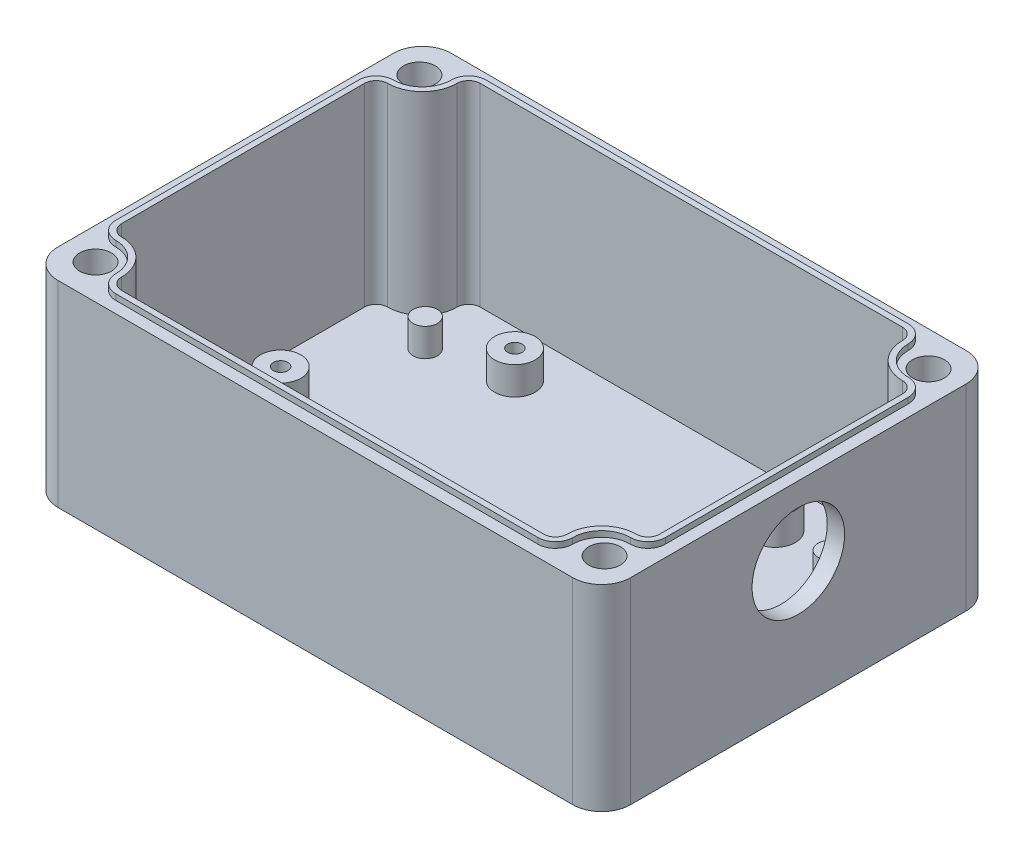
SolidWorks part; units mm, degrees
ref_plane "Plan de face" through (0, 0, 0) normal (0, 0, 1) x (1, 0, 0)
ref_plane "Plan de dessus" through (0, 0, 0) normal (0, 1, 0) x (1, 0, 0)
ref_plane "Plan de droite" through (0, 0, 0) normal (1, 0, 0) x (0, 0, -1)
sketch "Esquisse1" plane through (0, 0, 0) normal (0, 1, 0) x (1, 0, 0)
  line L1 (-44.5, 34) -> (44.5, 34)
  line L2 (-49.5, 29) -> (-49.5, -29)
  line L3 (-44.5, -34) -> (44.5, -34)
  line L4 (49.5, 29) -> (49.5, -29)
  arc A0 (49.5, 29) -> (44.5, 34) centre (44.5, 29) ccw
  arc A1 (44.5, -34) -> (49.5, -29) centre (44.5, -29) ccw
  arc A2 (-49.5, -29) -> (-44.5, -34) centre (-44.5, -29) ccw
  arc A3 (-49.5, 29) -> (-44.5, 34) centre (-44.5, 29) cw
  point P7 (49.5, 34)
  point P12 (-49.5, -34)
  point P15 (-49.5, 34)
  dimension "D5" = 5
  dimension "D1" = 68
  dimension "D2" = 99
  dimension "D3" = 49.5
  dimension "D4" = 34
extrude "Boss.-Extru.1" add sketch "Esquisse1" along normal blind 34
sketch "Esquisse2" plane through (0, 34, 0) normal (0, 1, 0) x (1, 0, 0)
  line L0 (-36.5, 31) -> (36.5, 31)
  line L1 (-46.5, 21) -> (-46.5, -21)
  line L2 (-36.5, -31) -> (36.5, -31)
  line L3 (46.5, 21) -> (46.5, -21)
  line L4 (-49.5, 29) -> (-49.5, -29) construction
  line L5 (49.5, -29) -> (49.5, 29) construction
  line L6 (-44.5, -34) -> (44.5, -34) construction
  line L7 (44.5, 34) -> (-44.5, 34) construction
  arc A0 (-44.5, -23) -> (-38.5, -29) centre (-44.5, -29) cw
  arc A1 (-38.5, 29) -> (-44.5, 23) centre (-44.5, 29) cw
  arc A2 (38.5, 29) -> (44.5, 23) centre (44.5, 29) ccw
  arc A3 (44.5, -23) -> (38.5, -29) centre (44.5, -29) ccw
  arc A4 (38.5, 29) -> (36.5, 31) centre (36.5, 29) ccw
  arc A5 (46.5, 21) -> (44.5, 23) centre (44.5, 21) ccw
  arc A6 (44.5, -23) -> (46.5, -21) centre (44.5, -21) ccw
  arc A7 (36.5, -31) -> (38.5, -29) centre (36.5, -29) ccw
  arc A8 (-38.5, -29) -> (-36.5, -31) centre (-36.5, -29) ccw
  arc A9 (-44.5, -23) -> (-46.5, -21) centre (-44.5, -21) cw
  arc A10 (-46.5, 21) -> (-44.5, 23) centre (-44.5, 21) cw
  arc A11 (-38.5, 29) -> (-36.5, 31) centre (-36.5, 29) cw
  point P26 (38.8431, 31)
  point P29 (46.5, 23.3431)
  point P32 (46.5, -23.3431)
  point P35 (38.8431, -31)
  point P38 (-38.8431, -31)
  point P41 (-46.5, -23.3431)
  point P44 (-46.5, 23.3431)
  point P47 (-38.8431, 31)
  dimension "D9" = 6
  dimension "D10" = 2
  dimension "D1" = 3
  dimension "D2" = 3
  dimension "D3" = 3
  dimension "D4" = 3
  dimension "D5" = 5
  dimension "D6" = 5
  dimension "D7" = 5
  dimension "D8" = 5
extrude "Enlèv. mat.-Extru.1" cut sketch "Esquisse2" against normal blind 32.5
sketch "Esquisse3" plane through (0, 34, 0) normal (0, 1, 0) x (1, 0, 0)
  circle A0 centre (-44, 28) radius 2.75
  circle A1 centre (-44, -28) radius 2.75
  circle A2 centre (44, -28) radius 2.75
  circle A3 centre (44, 28) radius 2.75
  dimension "D1" = 5.5
  dimension "D2" = 28
  dimension "D3" = 56
  dimension "D4" = 88
  dimension "D5" = 44
extrude "Enlèv. mat.-Extru.2" cut sketch "Esquisse3" against normal up to next
sketch "Esquisse4" plane through (0, 34, 0) normal (0, 1, 0) x (1, 0, 0)
  line L4 (46.5, -21) -> (46.5, 21)
  line L5 (36.5, 31) -> (-36.5, 31)
  line L6 (-46.5, 21) -> (-46.5, -21)
  line L7 (-36.5, -31) -> (36.5, -31)
  line L8 (47.5, -21) -> (47.5, 21)
  line L9 (-36.5, -32) -> (36.5, -32)
  line L10 (-47.5, 21) -> (-47.5, -21)
  line L11 (36.5, 32) -> (-36.5, 32)
  line L12 (47.5, -21) -> (47.5, 21)
  line L13 (-36.5, -32) -> (36.5, -32)
  line L14 (-47.5, 21) -> (-47.5, -21)
  line L15 (36.5, 32) -> (-36.5, 32)
  arc A12 (46.5, 21) -> (44.5, 23) centre (44.5, 21) ccw
  arc A13 (38.5, 29) -> (44.5, 23) centre (44.5, 29) ccw
  arc A14 (38.5, 29) -> (36.5, 31) centre (36.5, 29) ccw
  arc A15 (-36.5, 31) -> (-38.5, 29) centre (-36.5, 29) ccw
  arc A16 (-44.5, 23) -> (-38.5, 29) centre (-44.5, 29) ccw
  arc A17 (-44.5, 23) -> (-46.5, 21) centre (-44.5, 21) ccw
  arc A18 (-46.5, -21) -> (-44.5, -23) centre (-44.5, -21) ccw
  arc A19 (-38.5, -29) -> (-44.5, -23) centre (-44.5, -29) ccw
  arc A20 (-38.5, -29) -> (-36.5, -31) centre (-36.5, -29) ccw
  arc A21 (36.5, -31) -> (38.5, -29) centre (36.5, -29) ccw
  arc A22 (44.5, -23) -> (38.5, -29) centre (44.5, -29) ccw
  arc A23 (44.5, -23) -> (46.5, -21) centre (44.5, -21) ccw
  arc A24 (39.5, 29) -> (36.5, 32) centre (36.5, 29) ccw
  arc A25 (39.5, 29) -> (44.5, 24) centre (44.5, 29) ccw
  arc A26 (47.5, 21) -> (44.5, 24) centre (44.5, 21) ccw
  arc A27 (44.5, -24) -> (47.5, -21) centre (44.5, -21) ccw
  arc A28 (44.5, -24) -> (39.5, -29) centre (44.5, -29) ccw
  arc A29 (36.5, -32) -> (39.5, -29) centre (36.5, -29) ccw
  arc A30 (-39.5, -29) -> (-36.5, -32) centre (-36.5, -29) ccw
  arc A31 (-39.5, -29) -> (-44.5, -24) centre (-44.5, -29) ccw
  arc A32 (-47.5, -21) -> (-44.5, -24) centre (-44.5, -21) ccw
  arc A33 (-44.5, 24) -> (-47.5, 21) centre (-44.5, 21) ccw
  arc A34 (-44.5, 24) -> (-39.5, 29) centre (-44.5, 29) ccw
  arc A35 (-36.5, 32) -> (-39.5, 29) centre (-36.5, 29) ccw
  arc A36 (39.5, 29) -> (36.5, 32) centre (36.5, 29) ccw
  arc A37 (39.5, 29) -> (44.5, 24) centre (44.5, 29) ccw
  arc A38 (47.5, 21) -> (44.5, 24) centre (44.5, 21) ccw
  arc A39 (44.5, -24) -> (47.5, -21) centre (44.5, -21) ccw
  arc A40 (44.5, -24) -> (39.5, -29) centre (44.5, -29) ccw
  arc A41 (36.5, -32) -> (39.5, -29) centre (36.5, -29) ccw
  arc A42 (-39.5, -29) -> (-36.5, -32) centre (-36.5, -29) ccw
  arc A43 (-39.5, -29) -> (-44.5, -24) centre (-44.5, -29) ccw
  arc A44 (-47.5, -21) -> (-44.5, -24) centre (-44.5, -21) ccw
  arc A45 (-44.5, 24) -> (-47.5, 21) centre (-44.5, 21) ccw
  arc A46 (-44.5, 24) -> (-39.5, 29) centre (-44.5, 29) ccw
  arc A47 (-36.5, 32) -> (-39.5, 29) centre (-36.5, 29) ccw
  dimension "D1" = 1
  dimension "D2" = 1
extrude "Boss.-Extru.2" add sketch "Esquisse4" along normal blind 1
sketch "Esquisse5" plane through (0, 0, 0) normal (0, -1, 0) x (1, 0, 0)
  circle A0 centre (-44, 28) radius 3.4
  circle A1 centre (44, 28) radius 3.4
  circle A2 centre (44, -28) radius 3.4
  circle A3 centre (-44, -28) radius 3.4
  dimension "D1" = 6.8
extrude "Enlèv. mat.-Extru.3" cut sketch "Esquisse5" against normal blind 25
sketch "Esquisse6" plane through (0, 1.5, 0) normal (0, 1, 0) x (1, 0, 0)
  line L0 (0, -19.25) -> (0, 19.25) construction
  line L1 (-19.25, 0) -> (19.25, 0) construction
  circle A0 centre (-22.5, 23) radius 3.5
  circle A1 centre (-22.5, 23) radius 1.25
  circle A2 centre (-40, 0) radius 3.5
  circle A3 centre (-40, 0) radius 1.25
  circle A4 centre (-35, 20) radius 2.1
  circle A5 centre (35, 20) radius 2.1
  circle A6 centre (40, 0) radius 1.25
  circle A7 centre (40, 0) radius 3.5
  circle A8 centre (22.5, 23) radius 1.25
  circle A9 centre (22.5, 23) radius 3.5
  circle A10 centre (22.5, -23) radius 3.5
  circle A11 centre (22.5, -23) radius 1.25
  circle A12 centre (35, -20) radius 2.1
  circle A13 centre (-35, -20) radius 2.1
  circle A14 centre (-22.5, -23) radius 1.25
  circle A15 centre (-22.5, -23) radius 3.5
  dimension "D1" = 7
  dimension "D2" = 2.5
  dimension "D3" = 4.2
  dimension "D4" = 2.5
  dimension "D5" = 7
  dimension "D6" = 40
  dimension "D7" = 23
  dimension "D8" = 22.5
  dimension "D9" = 20
  dimension "D10" = 35
extrude "Boss.-Extru.3" add sketch "Esquisse6" along normal blind 4.85
sketch "Esquisse7" plane through (49.5, 0, 0) normal (1, 0, 0) x (0, 0, -1)
  circle A0 centre (0, 22) radius 8
  dimension "D1" = 16
  dimension "D2" = 22
extrude "Enlèv. mat.-Extru.4" cut sketch "Esquisse7" against normal up to next
